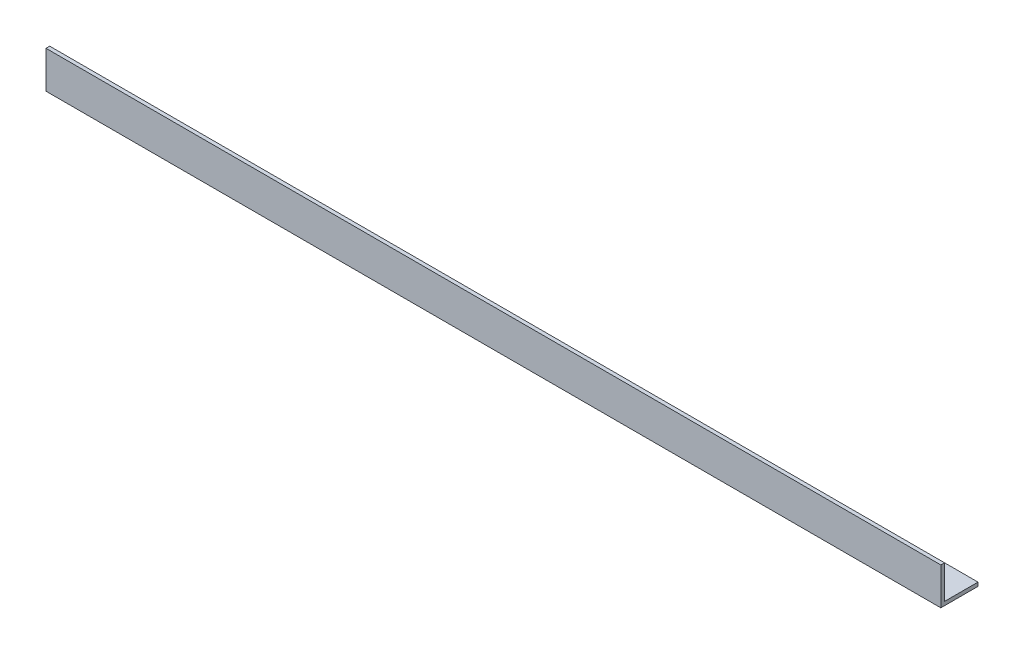
SolidWorks part; units mm, degrees
ref_plane "Спереди" through (0, 0, 0) normal (0, 0, 1) x (1, 0, 0)
ref_plane "Сверху" through (0, 0, 0) normal (0, 1, 0) x (1, 0, 0)
ref_plane "Справа" through (0, 0, 0) normal (1, 0, 0) x (0, 0, -1)
sketch "Эскиз1" plane through (0, 0, 0) normal (1, 0, 0) x (0, 0, -1)
  line L0 (0, 0) -> (0, 15)
  line L1 (0, 15) -> (1.5, 15)
  line L2 (1.5, 15) -> (1.5, 1.5)
  line L3 (1.5, 1.5) -> (15, 1.5)
  line L4 (15, 1.5) -> (15, 0)
  line L5 (15, 0) -> (0, 0)
  dimension "D1" = 15
  dimension "D2" = 15
  dimension "D3" = 1.5
  dimension "D4" = 1.5
extrude "Бобышка-Вытянуть1" add sketch "Эскиз1" along normal blind 361
